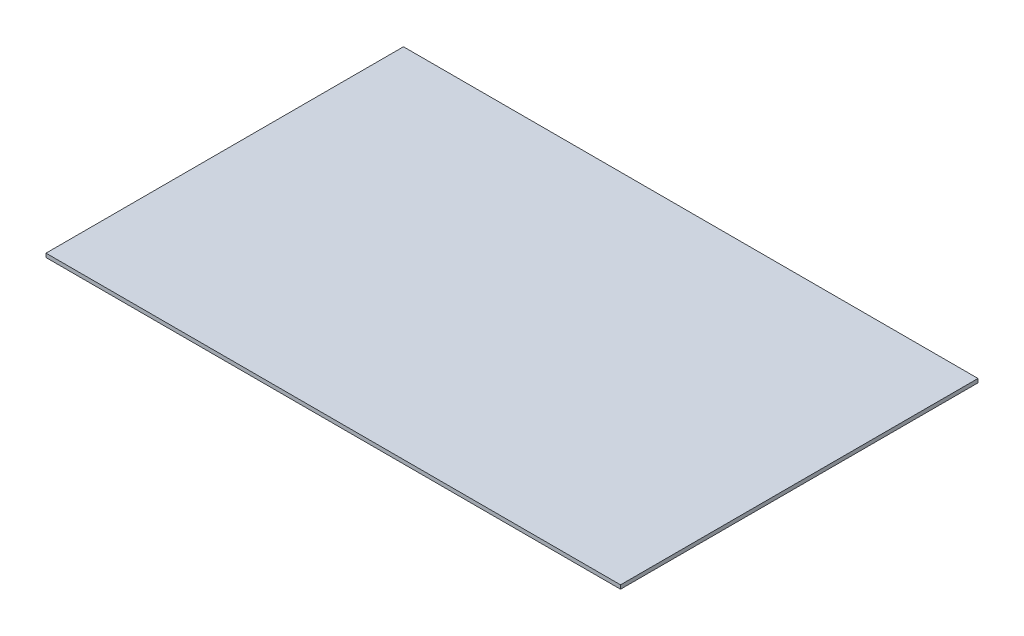
SolidWorks part; units mm, degrees
ref_plane "Front Plane" through (0, 0, 0) normal (0, 0, 1) x (1, 0, 0)
ref_plane "Top Plane" through (0, 0, 0) normal (0, 1, 0) x (1, 0, 0)
ref_plane "Right Plane" through (0, 0, 0) normal (1, 0, 0) x (0, 0, -1)
sketch "Sketch1" plane through (0, 0, 0) normal (0, 1, 0) x (1, 0, 0)
  line L1 (-225, -140) -> (225, -140)
  line L2 (-225, -140) -> (-225, 140)
  line L3 (-225, 140) -> (225, 140)
  line L4 (225, -140) -> (225, 140)
  line L5 (-225, -140) -> (225, 140) construction
  line L6 (-225, 140) -> (225, -140) construction
  point P0 (0, 0)
  dimension "D1" = 280
  dimension "D2" = 450
extrude "Boss-Extrude1" add sketch "Sketch1" along normal blind 3
